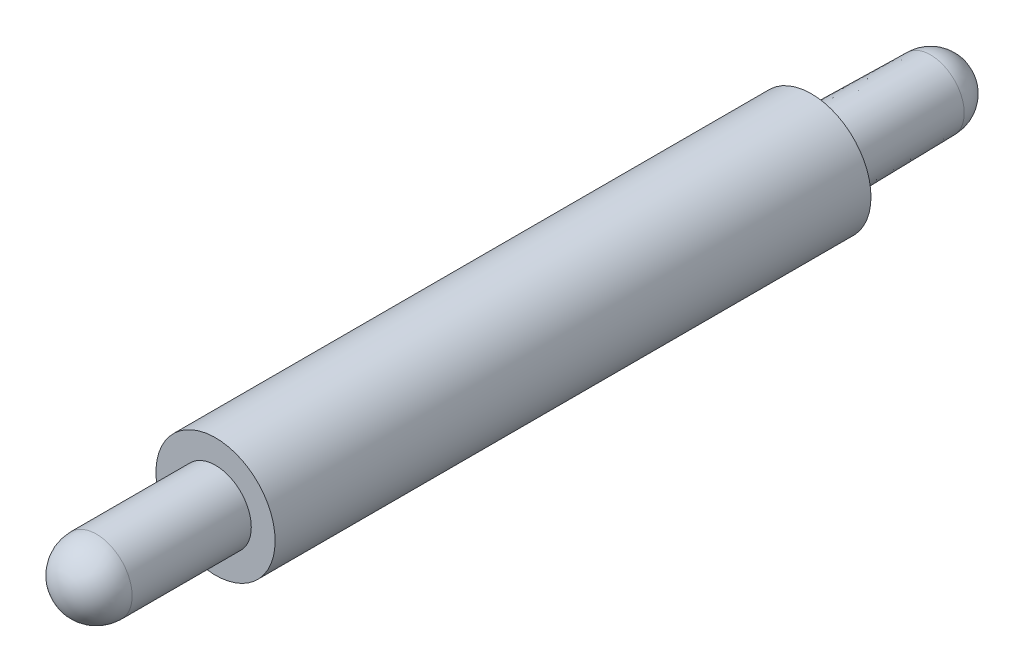
SolidWorks part; units mm, degrees
ref_plane "Front Plane" through (0, 0, 0) normal (0, 0, 1) x (1, 0, 0)
ref_plane "Top Plane" through (0, 0, 0) normal (0, 1, 0) x (1, 0, 0)
ref_plane "Right Plane" through (0, 0, 0) normal (1, 0, 0) x (0, 0, -1)
sketch "Sketch2" plane through (0, 0, 0) normal (0, 0, 1) x (1, 0, 0)
  circle A0 centre (0, 0) radius 5
  dimension "D1" = 10
extrude "Boss-Extrude1" add sketch "Sketch2" along normal blind 50
sketch "Sketch3" plane through (0, 0, 0) normal (0, 0, -1) x (-1, 0, 0)
  circle A0 centre (0, 0) radius 3
  dimension "D1" = 6
extrude "Boss-Extrude2" add sketch "Sketch3" along normal blind 10 draft 1
sketch "Sketch4" plane through (0, 0, -10) normal (0, 0, -1) x (-1, 0, 0)
  line L0 (0, 2.8254) -> (0, -2.8254)
  circle A0 centre (0, 0) radius 2.8254 construction
  arc A1 (0, -2.8254) -> (0, 2.8254) centre (0, 0) cw
revolve "Revolve1" add sketch "Sketch4" angle 360 about L0
sketch "Sketch5" plane through (0, 0, 50) normal (0, 0, 1) x (1, 0, 0)
  circle A0 centre (0, 0) radius 3
  dimension "D1" = 6
extrude "Boss-Extrude3" add sketch "Sketch5" along normal blind 10
sketch "Sketch6" plane through (0, 0, 60) normal (0, 0, 1) x (1, 0, 0)
  line L0 (0, 3) -> (0, -3)
  circle A0 centre (0, 0) radius 3 construction
  arc A1 (0, -3) -> (0, 3) centre (0, 0) cw
  dimension "D1" = 3
revolve "Revolve2" add sketch "Sketch6" angle 360 about L0
